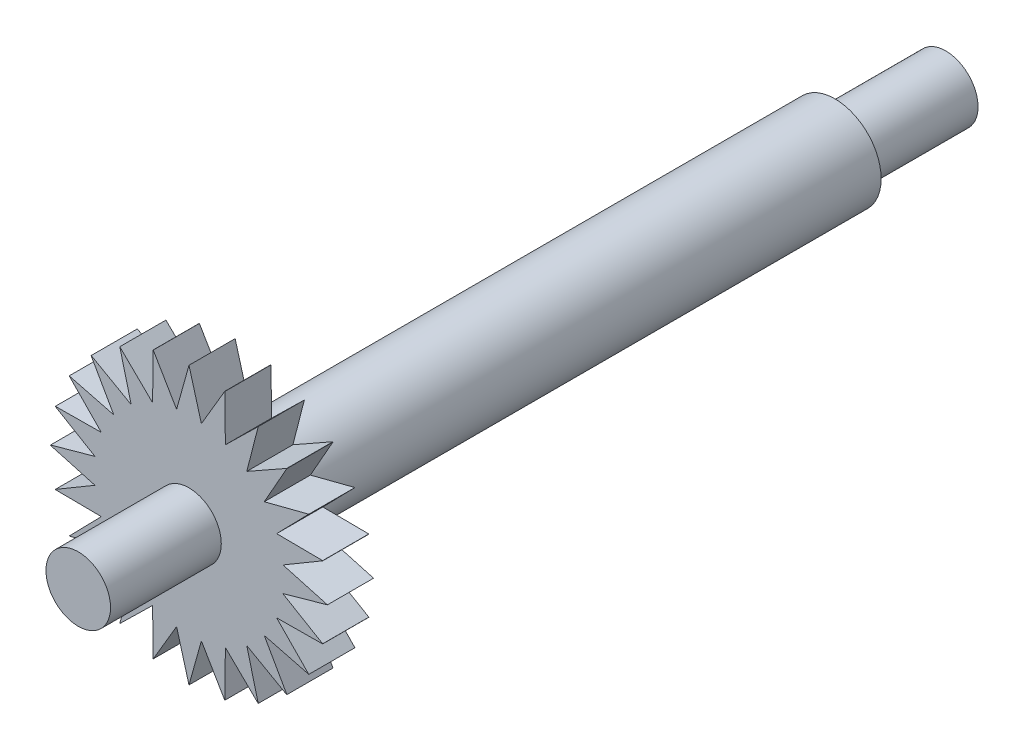
SolidWorks part; units mm, degrees
material "ABS"
ref_plane "Plan de face" through (0, 0, 0) normal (0, 0, 1) x (1, 0, 0)
ref_plane "Plan de dessus" through (0, 0, 0) normal (0, 1, 0) x (1, 0, 0)
ref_plane "Plan de droite" through (0, 0, 0) normal (1, 0, 0) x (0, 0, -1)
sketch "Esquisse1" plane through (0, 0, 0) normal (0, 0, 1) x (1, 0, 0)
  circle A0 centre (0, 0) radius 5
  dimension "D1" = 10
extrude "Boss.-Extru.2" add sketch "Esquisse1" along normal blind 70
sketch "Esquisse2" plane through (0, 0, 0) normal (0, 0, -1) x (-1, 0, 0)
  circle A0 centre (0, 0) radius 3.5
  dimension "D1" = 7
extrude "Boss.-Extru.3" add sketch "Esquisse2" along normal blind 12
sketch "Esquisse4" plane through (0, 0, 70) normal (0, 0, 1) x (1, 0, 0)
  circle A0 centre (0, 0) radius 15
  dimension "D1" = 30
extrude "Boss.-Extru.5" add sketch "Esquisse4" against normal blind 5
sketch "Esquisse5" plane through (0, 0, 70) normal (0, 0, 1) x (1, 0, 0)
  circle A0 centre (0, 0) radius 3.5
  dimension "D1" = 7
extrude "Boss.-Extru.6" add sketch "Esquisse5" along normal blind 12
sketch "Esquisse6" plane through (0, 0, 70) normal (0, 0, 1) x (1, 0, 0)
  line L0 (0, 10) -> (0, -10) construction
  line L1 (-10, 0) -> (10, 0) construction
  line L2 (0, 10) -> (0, 15) construction
  line L3 (10, 0) -> (15, 0) construction
  line L4 (15, 0) -> (-15, 0) construction
  line L5 (0, -10) -> (0, -15) construction
  line L6 (0, 15) -> (1.425, 9.8979)
  line L7 (0, 15) -> (-1.425, 9.8979)
  line L8 (0, 0) -> (-3.8907, 14.5215) construction
  line L9 (0, 0) -> (-7.5126, 13.022) construction
  line L10 (0, 0) -> (-10.6237, 10.6372) construction
  line L11 (0, 0) -> (-13.0125, 7.5291) construction
  line L12 (0, 0) -> (-14.5165, 3.9092) construction
  line L13 (-3.8907, 14.5215) -> (-1.1901, 9.9289)
  line L14 (-3.8907, 14.5215) -> (-3.9427, 9.19)
  line L15 (-7.4994, 12.9907) -> (-6.1827, 7.8596)
  line L16 (-7.4994, 12.9907) -> (-3.7145, 9.2845)
  line L17 (-14.5165, 3.9092) -> (-9.1849, 3.9543)
  line L18 (-14.5165, 3.9092) -> (-9.9274, 1.2028)
  line L19 (-10.6237, 10.6372) -> (-7.9997, 6.0004)
  line L20 (-10.6237, 10.6372) -> (-5.9821, 8.0134)
  line L21 (-12.9812, 7.516) -> (-7.8518, 6.1927)
  line L22 (-12.9812, 7.516) -> (-9.2798, 3.7263)
  line L23 (-15, 0.0191) -> (-9.8961, 1.4376)
  line L24 (-15, 0.0191) -> (-9.8998, -1.4124)
  line L25 (-15, -0.0191) -> (-9.8961, -1.4376)
  line L26 (-14.5165, -3.9092) -> (-9.9274, -1.2028)
  line L27 (-14.5165, -3.9092) -> (-9.1849, -3.9543)
  line L28 (-12.9812, -7.516) -> (-9.2798, -3.7263)
  line L29 (-12.9812, -7.516) -> (-7.8518, -6.1927)
  line L30 (-10.6237, -10.6372) -> (-7.9997, -6.0004)
  line L31 (-10.6237, -10.6372) -> (-5.9821, -8.0134)
  line L32 (-7.4994, -12.9907) -> (-6.1827, -7.8596)
  line L33 (-7.4994, -12.9907) -> (-3.7145, -9.2845)
  line L34 (-3.8907, -14.5215) -> (-3.9427, -9.19)
  line L35 (-3.8907, -14.5215) -> (-1.1901, -9.9289)
  line L36 (0, -15) -> (-1.425, -9.8979)
  line L37 (0, -15) -> (1.425, -9.8979)
  line L38 (3.8907, -14.5215) -> (1.1901, -9.9289)
  line L39 (3.8907, -14.5215) -> (3.9427, -9.19)
  line L40 (7.4994, -12.9907) -> (3.7145, -9.2845)
  line L41 (7.4994, -12.9907) -> (6.1827, -7.8596)
  line L42 (10.6237, -10.6372) -> (5.9821, -8.0134)
  line L43 (10.6237, -10.6372) -> (7.9997, -6.0004)
  line L44 (12.9812, -7.516) -> (7.8518, -6.1927)
  line L45 (12.9812, -7.516) -> (9.2798, -3.7263)
  line L46 (14.5165, -3.9092) -> (9.1849, -3.9543)
  line L47 (14.5165, -3.9092) -> (9.9274, -1.2028)
  line L48 (15, 0.0191) -> (9.8998, -1.4124)
  line L49 (15, 0.0191) -> (9.8961, 1.4376)
  line L50 (14.5165, 3.9092) -> (9.9274, 1.2028)
  line L51 (14.5165, 3.9092) -> (9.1849, 3.9543)
  line L52 (12.9812, 7.516) -> (9.2798, 3.7263)
  line L53 (12.9812, 7.516) -> (7.8518, 6.1927)
  line L54 (10.6237, 10.6372) -> (7.9997, 6.0004)
  line L55 (10.6237, 10.6372) -> (5.9821, 8.0134)
  line L56 (7.4994, 12.9907) -> (6.1827, 7.8596)
  line L57 (7.4994, 12.9907) -> (3.7145, 9.2845)
  line L58 (0, 15) -> (1.425, 9.8979)
  line L59 (3.8907, 14.5215) -> (3.9427, 9.19)
  line L60 (3.8907, 14.5215) -> (1.1901, 9.9289)
  circle A0 centre (0, 0) radius 10
  circle A1 centre (0, 0) radius 15 construction
  circle A2 centre (0, 0) radius 15.0337
  circle M35 centre (0, 0) radius 15
  dimension "D3" = 1.425
  dimension "D4" = 3.92
  dimension "D8" = 3.92
  dimension "D9" = 2.85
  dimension "D10" = 1.43
extrude "Enlèv. mat.-Extru.1" cut sketch "Esquisse6" against normal blind 12 contours L20 L15 M35 | L21 L19 M35 | L22 L17 M35 | L23 L18 M35 | L26 L25 M35 | L28 L27 M35 | L30 L29 M35 | L32 L31 M35 | L34 L33 M35 | L36 L35 M35 | L38 L37 M35 | L40 L39 M35 | L42 L41 M35 | L44 L43 M35 | L46 L45 M35 | L48 L47 M35 | L50 L49 M35 | L52 L51 M35 | L54 L53 M35 | L56 L55 M35 | L59 L57 M35 | L60 L6 M35 | L13 L7 M35 | L16 L14 M35
